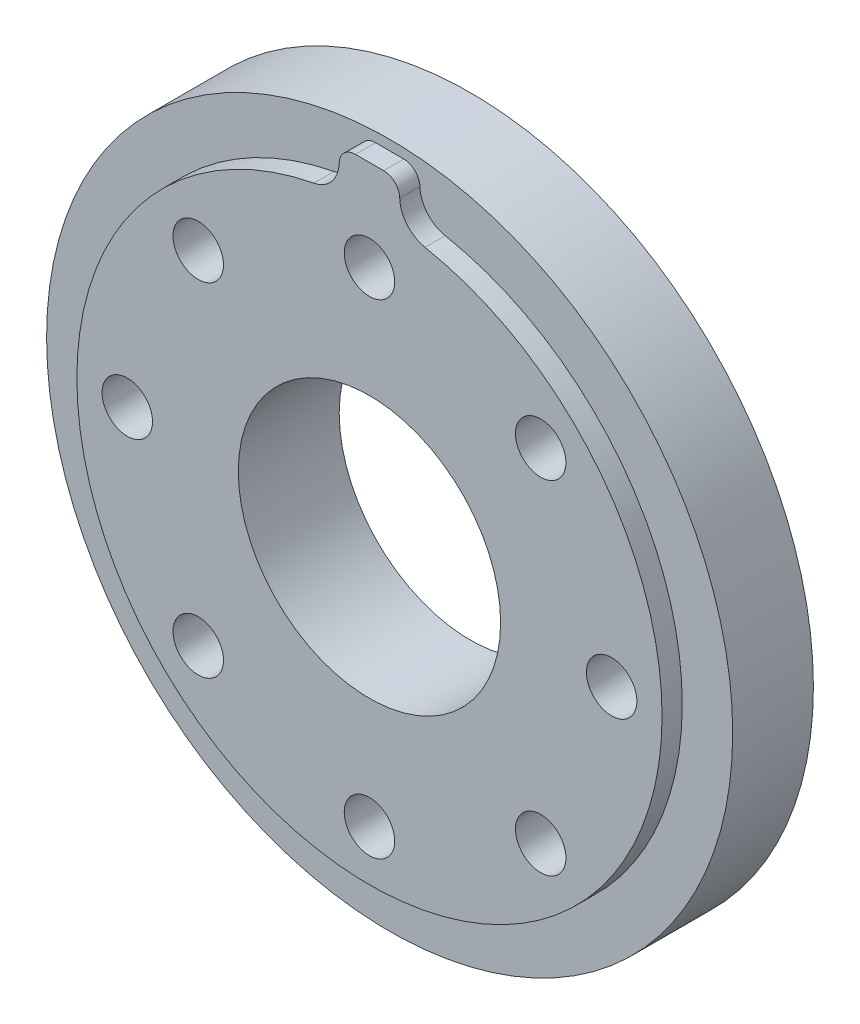
SolidWorks part; units mm, degrees
ref_plane "正面" through (0, 0, 0) normal (0, 0, 1) x (1, 0, 0)
ref_plane "平面" through (0, 0, 0) normal (0, 1, 0) x (1, 0, 0)
ref_plane "右側面" through (0, 0, 0) normal (1, 0, 0) x (0, 0, -1)
sketch "ｽｹｯﾁ1" plane through (0, 0, 0) normal (0, 0, 1) x (1, 0, 0)
  circle A0 centre (0, 0) radius 17
  dimension "D1" = 34
extrude "ﾎﾞｽ - 押し出し1" add sketch "ｽｹｯﾁ1" along normal blind 4
sketch "ｽｹｯﾁ2" plane through (0, 0, 4) normal (0, 0, 1) x (1, 0, 0)
  line L1 (-1.5, 12.5) -> (1.5, 12.5)
  line L2 (-1.5, 12.5) -> (-1.5, 16.5)
  line L3 (-1.5, 16.5) -> (1.5, 16.5)
  line L4 (1.5, 12.5) -> (1.5, 16.5)
  line L5 (-1.5, 12.5) -> (1.5, 16.5) construction
  line L6 (-1.5, 16.5) -> (1.5, 12.5) construction
  circle A0 centre (0, 0) radius 14.5
  point P3 (0, 14.5)
  circle M5 centre (0, 0) radius 17
  dimension "D1" = 29
  dimension "D2" = 2
  dimension "D3" = 3
extrude "ﾎﾞｽ - 押し出し2" add sketch "ｽｹｯﾁ2" along normal blind 1 contours A0 L4 L2 M5 | L4 L3 L2 M5 | L2 A0 L4 L1 | L4 A0 L2 L1
fillet "ﾌｨﾚｯﾄ1" radius 1.55 2 edges at (-1.5, 14.4222, 4.5) (1.5, 14.4222, 4.5)
fillet "ﾌｨﾚｯﾄ2" radius 0.8 2 edges at (1.5, 16.5, 4.5) (-1.5, 16.5, 4.5)
sketch "ｽｹｯﾁ3" plane through (0, 0, 5) normal (0, 0, 1) x (1, 0, 0)
  circle A0 centre (0, 0) radius 6.5
  dimension "D1" = 13
extrude "ｶｯﾄ - 押し出し1" cut sketch "ｽｹｯﾁ3" against normal through all
sketch "ｽｹｯﾁ4" plane through (0, 0, 0) normal (0, 0, -1) x (-1, 0, 0)
  circle A0 centre (0, 0) radius 12 construction
  circle A1 centre (0, 12) radius 1.25
  circle A2 centre (12, 0) radius 1.25
  circle A3 centre (0, -12) radius 1.25
  circle A4 centre (-12, 0) radius 1.25
  point P14 (0, 0)
  dimension "D1" = 24
  dimension "D2" = 2.5
  dimension "D3" = 4
extrude "ｶｯﾄ - 押し出し2" cut sketch "ｽｹｯﾁ4" against normal through all
pattern_circular "円形ﾊﾟﾀｰﾝ1" count 2 over 45 about axis through (0, 0, 0) along (0, 0, 1) of "ｶｯﾄ - 押し出し2"
